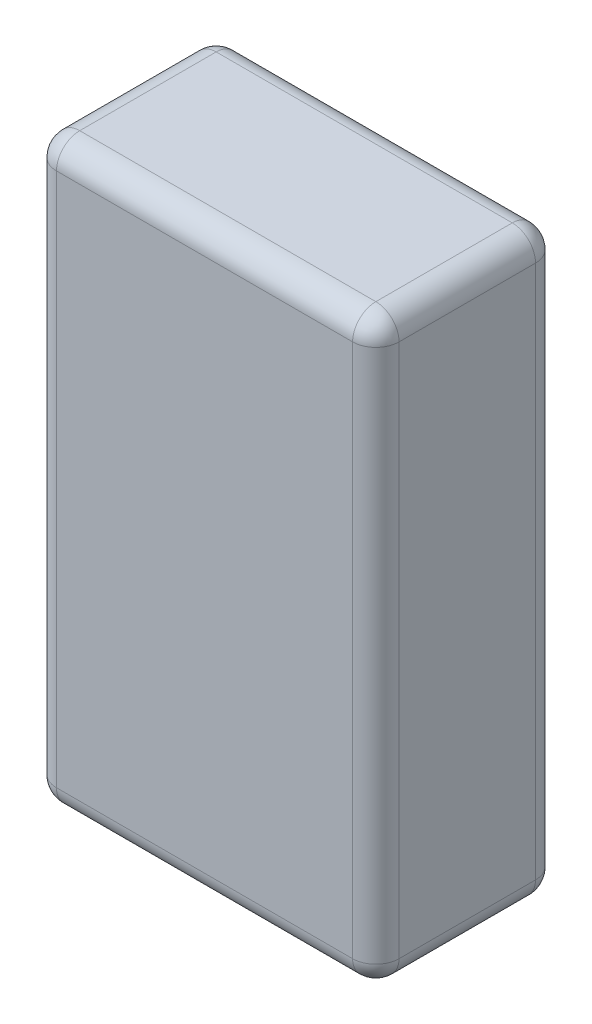
SolidWorks part; units mm, degrees
ref_plane "Front Plane" through (0, 0, 0) normal (0, 0, 1) x (1, 0, 0)
ref_plane "Top Plane" through (0, 0, 0) normal (0, 1, 0) x (1, 0, 0)
ref_plane "Right Plane" through (0, 0, 0) normal (1, 0, 0) x (0, 0, -1)
sketch "Sketch1" plane through (0, 0, 0) normal (0, 1, 0) x (1, 0, 0)
  line L1 (0, 0) -> (29.972, 0)
  line L2 (0, 0) -> (0, 16.002)
  line L3 (0, 16.002) -> (29.972, 16.002)
  line L4 (29.972, 0) -> (29.972, 16.002)
  dimension "D1" = 29.972
  dimension "D2" = 16.002
extrude "Boss-Extrude1" add sketch "Sketch1" along normal blind 50.8
fillet "Fillet1" radius 2.032 12 edges at (0, 0, -8.001) (0, 25.4, -16.002) (14.986, 0, -16.002) (29.972, 25.4, -16.002) (29.972, 0, -8.001) (0, 25.4, 0) (29.972, 25.4, 0) (14.986, 0, 0) (14.986, 50.8, -16.002) (29.972, 50.8, -8.001) (14.986, 50.8, 0) (0, 50.8, -8.001)
